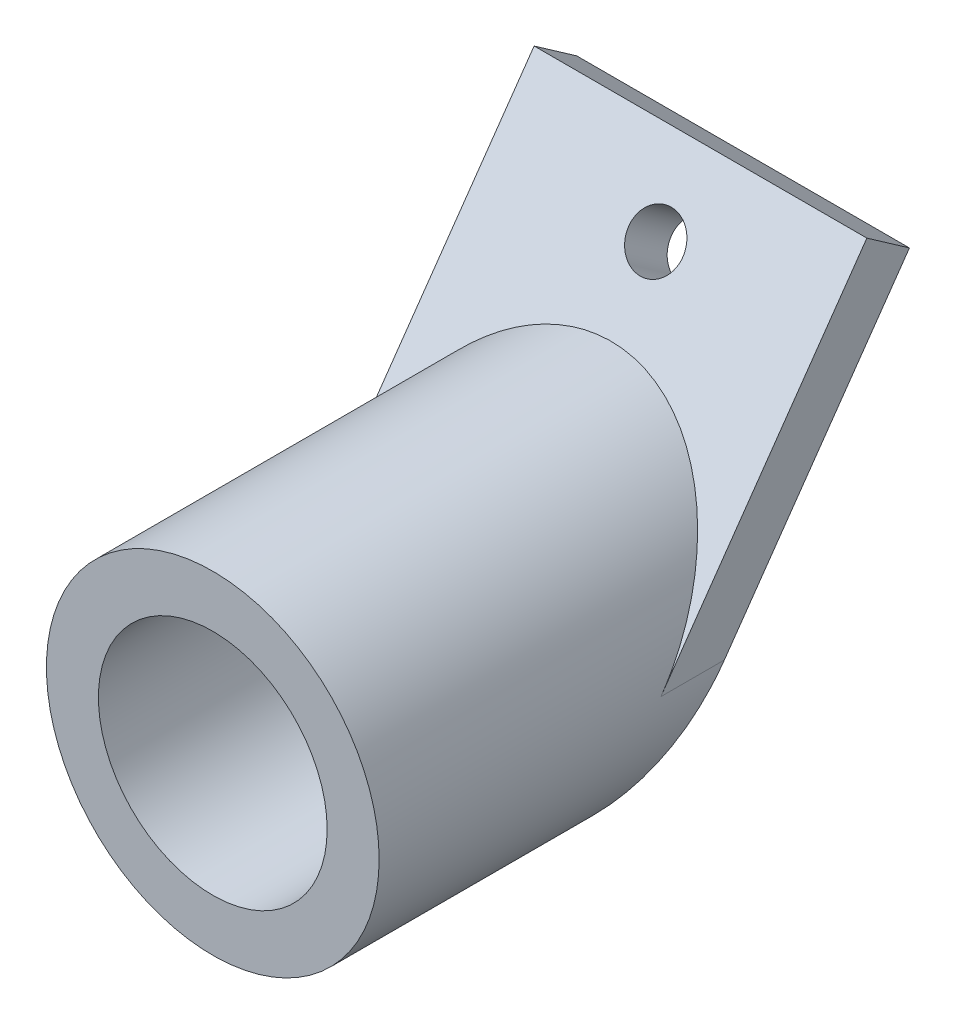
SolidWorks part; units mm, degrees
ref_plane "Front Plane" through (0, 0, 0) normal (0, 0, 1) x (1, 0, 0)
ref_plane "Top Plane" through (0, 0, 0) normal (0, 1, 0) x (1, 0, 0)
ref_plane "Right Plane" through (0, 0, 0) normal (1, 0, 0) x (0, 0, -1)
sketch "Sketch1" plane through (0, 0, 0) normal (0, 0, 1) x (1, 0, 0)
  circle A0 centre (0, 0) radius 11
  circle A1 centre (0, 0) radius 16
extrude "Boss-Extrude1" add sketch "Sketch1" along normal blind 20
sketch "Sketch2" plane through (0, 0, 0) normal (0, 0, -1) x (-1, 0, 0)
  circle A0 centre (0, 0) radius 16
extrude "Boss-Extrude2" add sketch "Sketch2" along normal blind 2
sketch "Sketch3" plane through (0, 0, 0) normal (1, 0, 0) x (0, 0, -1)
  line L5 (31.0022, 25.4194) -> (26.9064, 28.2873)
  line L7 (2, -16) -> (2, 16) construction
  line L8 (2, -7.2828) -> (2, -16)
  line L9 (18.3028, 16) -> (2, -7.2828)
  line L10 (18.3028, 16) -> (26.9064, 28.2873)
  line L11 (31.0022, 25.4194) -> (2, -16)
extrude "Boss-Extrude3" add sketch "Sketch3" along normal through all and the other way through all
sketch "Sketch4" plane through (0, 0, -2) normal (0, 0, -1) x (-1, 0, 0)
  line L0 (16, 0) -> (34.2665, 0)
  line L1 (34.2665, 0) -> (32.1798, -27.298)
  line L2 (32.1798, -27.298) -> (-36.4631, -20.4887)
  line L3 (-36.4631, -20.4887) -> (-34.4306, 0)
  line L4 (-34.4306, 0) -> (-16, 0)
  circle A0 centre (0, 0) radius 16
  arc M11 (14.2464, -7.2828) -> (-14.2464, -7.2828) centre (0, 0) ccw
extrude "Cut-Extrude1" cut sketch "Sketch4" along normal through all contours A0 L4 L3 L2 L1 L0 M11
sketch "Sketch5" plane through (0, 0, -2) normal (0, 0, -1) x (-1, 0, 0)
  circle A0 centre (0, 0) radius 16
extrude "Boss-Extrude4" add sketch "Sketch5" along normal up to next
sketch "Sketch6" plane through (0, -3.3356, -4.7638) normal (0, 0.5736, 0.8192) x (1, 0, 0)
  line L0 (0, 38.6045) -> (0, 23.6045) construction
  line L1 (16, 38.6045) -> (-16, 38.6045) construction
  circle A0 centre (0, 31.1045) radius 2.6
  ellipse E0 centre (0, 4.0721) end of major axis (0, 23.6045) minor radius 16 (16, 4.0721) -> (-16, 4.0721) ccw construction
extrude "Cut-Extrude3" cut sketch "Sketch6" against normal through all
